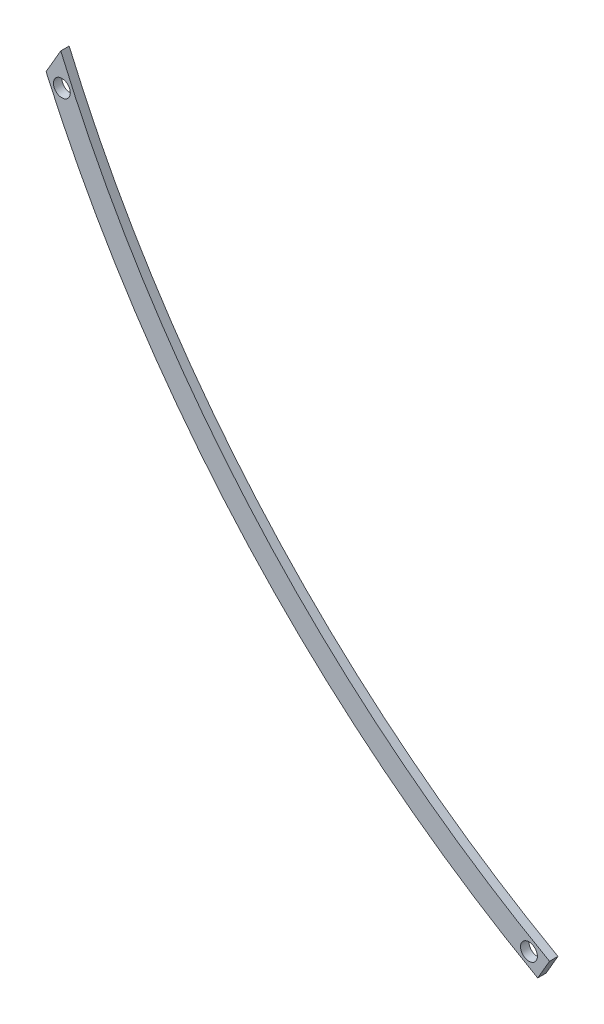
SolidWorks part; units mm, degrees
material "Plain Carbon Steel"
ref_plane "Front Plane" through (0, 0, 0) normal (0, 0, 1) x (1, 0, 0)
ref_plane "Top Plane" through (0, 0, 0) normal (0, 1, 0) x (1, 0, 0)
ref_plane "Right Plane" through (0, 0, 0) normal (1, 0, 0) x (0, 0, -1)
sketch "Sketch1" plane through (0, 0, 0) normal (0, 0, 1) x (1, 0, 0)
  line L3 (51.7632, -110.0875) -> (121.9945, 11.0398)
  line L5 (-2779.4684, 3240.603) -> (-2866.6361, 3090.2658)
  arc A0 (35.1118, 60.5571) -> (121.9945, 11.0398) centre (3412.3492, 5885.2474) ccw
  arc A1 (35.1118, 60.5571) -> (-2709.2063, 3081.8016) centre (3412.3492, 5885.2474) cw
  arc A2 (-2709.2063, 3081.8016) -> (-2779.4684, 3240.603) centre (3412.3492, 5885.2474) cw
  arc A3 (-2836.4932, 3023.5089) -> (-2866.6361, 3090.2658) centre (3412.3492, 5885.2474) cw
  arc A4 (-35.1118, -60.5571) -> (-2836.4932, 3023.5089) centre (3412.3492, 5885.2474) cw
  arc A5 (-35.1118, -60.5571) -> (51.7632, -110.0875) centre (3412.3492, 5885.2474) ccw
  arc A6 (-2836.4932, 3023.5089) -> (-3079.2092, 3627.5389) centre (3412.3492, 5885.2474) cw construction
  arc A7 (-2709.2063, 3081.8016) -> (-2946.9782, 3673.5277) centre (3412.3492, 5885.2474) cw construction
  arc A8 (-35.1118, -60.5571) -> (339.5635, -262.5625) centre (3412.3492, 5885.2474) ccw construction
  arc A9 (35.1118, 60.5571) -> (402.1552, -137.3336) centre (3412.3492, 5885.2474) ccw construction
  circle A10 centre (-2772.8497, 3052.6553) radius 50
  circle A11 centre (0, 0) radius 50
  dimension "D1" = 140
extrude "Boss-Extrude1" add sketch "Sketch1" along normal blind 50
